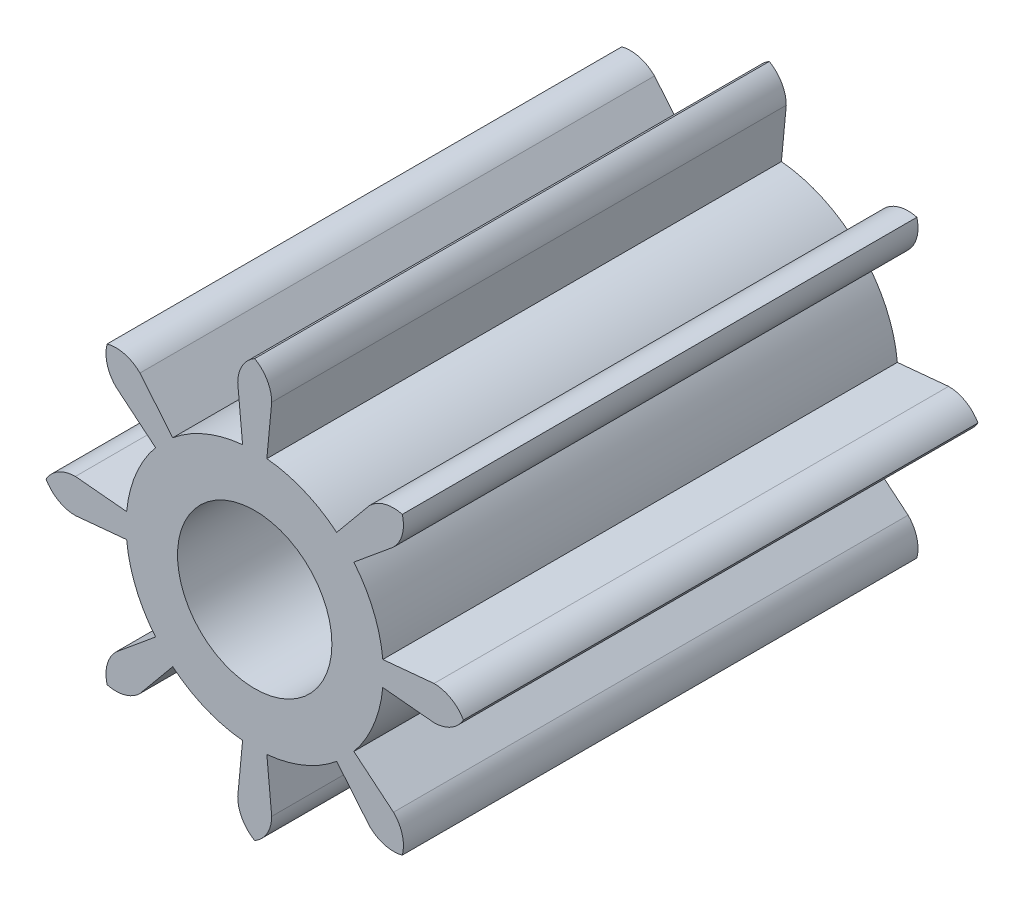
SolidWorks part; units mm, degrees
ref_plane "Front Plane" through (0, 0, 0) normal (0, 0, 1) x (1, 0, 0)
ref_plane "Top Plane" through (0, 0, 0) normal (0, 1, 0) x (1, 0, 0)
ref_plane "Right Plane" through (0, 0, 0) normal (1, 0, 0) x (0, 0, -1)
sketch "Sketch1" plane through (0, 0, 0) normal (0, 0, 1) x (1, 0, 0)
  line L0 (-0.55, 0) -> (0.55, 0) construction
  line L1 (-0.55, 0) -> (0.55, 0) construction
  line L2 (-0.33, 3.4844) -> (-0.2357, 2.4889)
  line L3 (-0.1414, 1.4933) -> (0, 0) construction
  line L4 (0, 0) -> (0.1414, 1.4933) construction
  line L5 (0.1414, 1.4933) -> (0.2357, 2.4889) construction
  line L6 (0, 4.056) -> (0, 3.5) construction
  line L7 (0, 3.5) -> (0, 2.5) construction
  line L8 (-0.2357, 2.4889) -> (-0.1414, 1.4933) construction
  line L9 (0.2357, 2.4889) -> (0.33, 3.4844)
  line L10 (-0.33, 7.0858) -> (0.33, 7.0858) construction
  circle A0 centre (0, 0) radius 3.5 construction
  arc A1 (-0.33, 3.4844) -> (0.33, 3.4844) centre (0, 0) ccw construction
  circle A2 centre (0, 0) radius 1.5
  arc A3 (0.33, 3.4844) -> (-0.33, 3.4844) centre (0, 0) ccw construction
  arc A4 (0, 4.056) -> (-0.33, 3.4844) centre (0.33, 3.4844) ccw
  arc A6 (0.33, 3.4844) -> (0, 4.056) centre (-0.33, 3.4844) ccw
  arc A7 (-0.2357, 2.4889) -> (0.2357, 2.4889) centre (0, 0) ccw
  arc A8 (0.2357, 2.4889) -> (-0.2357, 2.4889) centre (0, 0) ccw construction
  point P2 (0, 0)
  point P12 (0, 0)
  point P14 (0, 0)
  point P15 (0, 0)
  point P24 (0, 7.0858)
  dimension "D1" = 3
  dimension "D2" = 1
  dimension "D3" = 1.1
  dimension "D4" = 0.66
extrude "Boss-Extrude1" add sketch "Sketch1" against normal blind 10
pattern_circular "CirPattern1" count 8 over 360 about axis through (0, 0, 0) along (0, 0, 1) of "Boss-Extrude1"
equation "\"D4@Sketch1\"=\"D3@Sketch1\"*.6"
